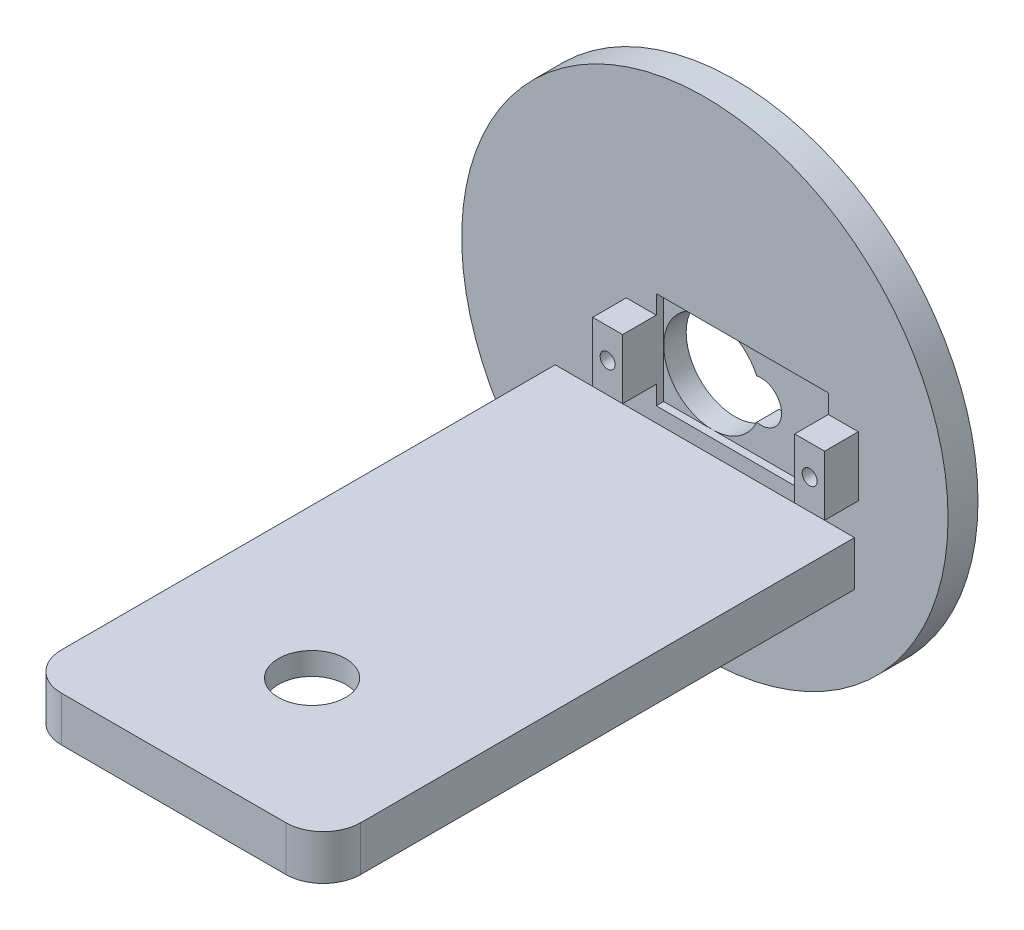
SolidWorks part; units mm, degrees
ref_plane "Plano frontal" through (0, 0, 0) normal (0, 0, 1) x (1, 0, 0)
ref_plane "Plano superior" through (0, 0, 0) normal (0, 1, 0) x (1, 0, 0)
ref_plane "Plano direito" through (0, 0, 0) normal (1, 0, 0) x (0, 0, -1)
sketch "Esboço1" plane through (0, 0, 0) normal (0, 0, 1) x (1, 0, 0)
  circle A0 centre (0, 0) radius 32.5
  arc A1 (5.9214, 2.6809) -> (5.9214, -2.6809) centre (0, 0) ccw
  arc A2 (5.9214, -2.6809) -> (5.9214, 2.6809) centre (6.5, 0) ccw
extrude "Ressalto-extrusão1" add sketch "Esboço1" along normal blind 4
sketch "Esboço2" plane through (0, 0, 4) normal (0, 0, 1) x (1, 0, 0)
  line L0 (-6.5, 0) -> (-8.5, 0) construction
  line L2 (-10.5, -4) -> (-6.5, -4)
  line L3 (-10.5, -4) -> (-10.5, 4)
  line L4 (-10.5, 4) -> (-6.5, 4)
  line L5 (-6.5, -4) -> (-6.5, 4)
  line L6 (-8.5, 4) -> (-8.5, -4) construction
  line L7 (-10.5, 0) -> (-6.5, 0) construction
  line L8 (16.5, 0) -> (9.075, 0) construction
  line L9 (16.5, -4) -> (20.5, -4)
  line L10 (16.5, -4) -> (16.5, 4)
  line L11 (16.5, 4) -> (20.5, 4)
  line L12 (20.5, -4) -> (20.5, 4)
  line L13 (18.5, 4) -> (18.5, -4) construction
  line L14 (16.5, 0) -> (20.5, 0) construction
  arc A0 (5.9214, 2.6809) -> (5.9214, -2.6809) centre (0, 0) ccw construction
  circle A1 centre (-8.5, 0) radius 1
  circle A2 centre (18.5, 0) radius 1
  arc A4 (5.9214, -2.6809) -> (5.9214, 2.6809) centre (6.5, 0) ccw construction
  dimension "D1" = 2
  dimension "D3" = 27
  dimension "D4" = 4
  dimension "D2" = 8
extrude "Ressalto-extrusão3" add sketch "Esboço2" along normal blind 4.5
sketch "Esboço3" plane through (0, 0, 4) normal (0, 0, 1) x (1, 0, 0)
  line L1 (-6.5, -6.5) -> (16.5, -6.5)
  line L2 (-6.5, -6.5) -> (-6.5, 6.5)
  line L3 (-6.5, 6.5) -> (16.5, 6.5)
  line L4 (16.5, -6.5) -> (16.5, 6.5)
  line L5 (5, 6.5) -> (5, -6.5) construction
  line L6 (-8.5, 0) -> (18.5, 0) construction
  line L7 (-6.5, 0) -> (16.5, 0) construction
  point P0 (5, 0)
  point P4 (5.575, -2.4952)
  dimension "D1" = 23
extrude "Corte-extrusão1" cut sketch "Esboço3" against normal blind 1
sketch "Esboço4" plane through (0, 0, 4) normal (0, 0, 1) x (1, 0, 0)
  line L0 (0, 0) -> (0, -11.5) construction
  line L2 (-20, -14.5) -> (20, -14.5)
  line L3 (-20, -14.5) -> (-20, -8.5)
  line L4 (-20, -8.5) -> (20, -8.5)
  line L5 (20, -14.5) -> (20, -8.5)
  line L6 (0, -8.5) -> (0, -14.5) construction
  line L7 (-20, -11.5) -> (20, -11.5) construction
extrude "Ressalto-extrusão4" add sketch "Esboço4" along normal blind 71
sketch "Esboço5" plane through (0, -14.5, 0) normal (0, -1, 0) x (1, 0, 0)
  line L0 (0, 4) -> (0, 56.5) construction
  line L2 (-20, 4) -> (20, 4) construction
  circle A0 centre (0, 56.5) radius 4.5
extrude "Corte-extrusão2" cut sketch "Esboço5" against normal blind 61
sketch "Esboço6" plane through (0, -14.5, 0) normal (0, -1, 0) x (1, 0, 0)
  line L0 (0, 56.5) -> (0, 4) construction
  line L2 (-20, 4) -> (20, 4) construction
  line L3 (0, 64.5) -> (-10.7031, 70.0325)
  line L4 (-8, 56.5) -> (-13.5325, 67.2031)
  line L5 (8, 56.5) -> (13.5325, 67.2031)
  line L6 (0, 64.5) -> (10.7031, 70.0325)
  line L7 (0, 48.5) -> (10.7031, 42.9675)
  line L8 (8, 56.5) -> (13.5325, 45.7969)
  line L9 (-8, 56.5) -> (-13.5325, 45.7969)
  line L10 (0, 48.5) -> (-10.7031, 42.9675)
  arc A0 (13.5325, 67.2031) -> (10.7031, 70.0325) centre (11.6673, 68.1673) ccw
  arc A1 (10.7031, 42.9675) -> (13.5325, 45.7969) centre (11.6673, 44.8327) ccw
  arc A2 (-13.5325, 45.7969) -> (-10.7031, 42.9675) centre (-11.6673, 44.8327) ccw
  arc A3 (-10.7031, 70.0325) -> (-13.5325, 67.2031) centre (-11.6673, 68.1673) ccw
  point P4 (0, 46.5)
  point P7 (0, 56.5)
  point P27 (0, 56.5)
  point P28 (0, 46.5)
  point P31 (0, 56.5)
extrude "Corte-extrusão3" cut sketch "Esboço6" against normal blind 3
fillet "Filete1" radius 5 2 edges at (-20, -11.5, 75) (20, -11.5, 75)
